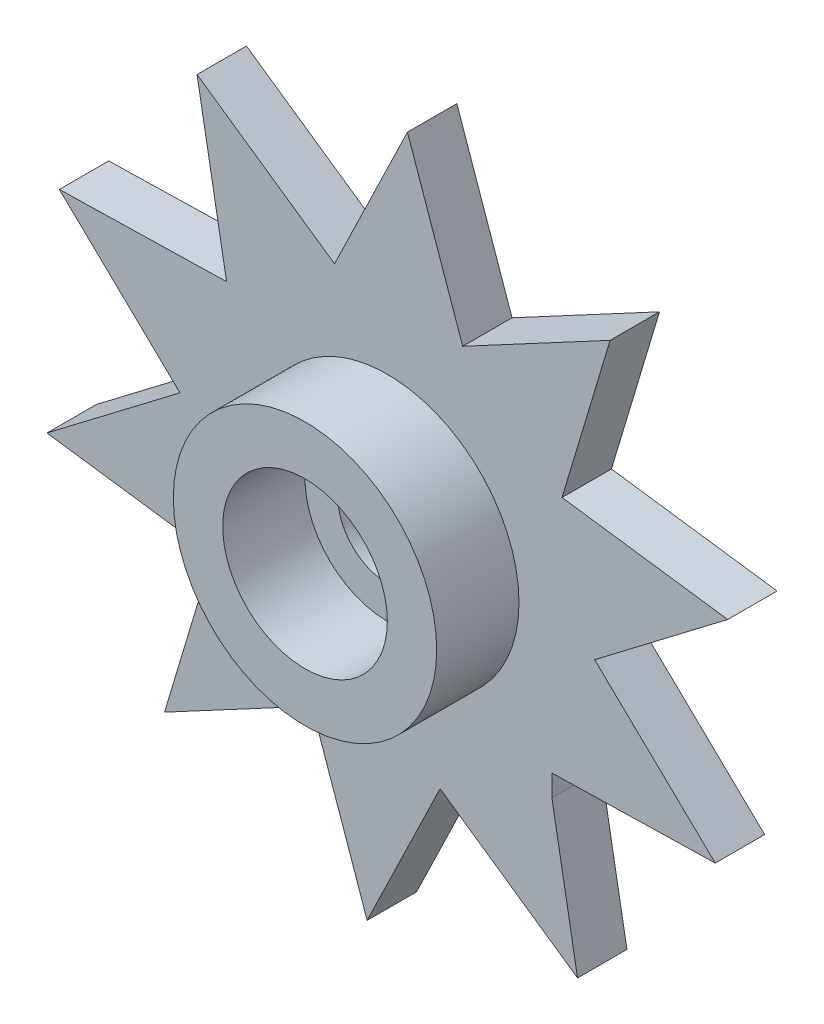
SolidWorks part; units mm, degrees
ref_plane "Plan de face" through (0, 0, 0) normal (0, 0, 1) x (1, 0, 0)
ref_plane "Plan de dessus" through (0, 0, 0) normal (0, 1, 0) x (1, 0, 0)
ref_plane "Plan de droite" through (0, 0, 0) normal (1, 0, 0) x (0, 0, -1)
sketch "Esquisse1" plane through (0, 0, 0) normal (0, 0, 1) x (1, 0, 0)
  line L0 (-27.0978, 20.4024) -> (-22.9222, 17.51)
  line L1 (-22.9222, 17.51) -> (-23.8175, 22.51)
  line L2 (-23.8175, 22.51) -> (-18.7392, 22.6243)
  line L3 (-18.7392, 22.6243) -> (-22.4024, 26.1432)
  line L4 (-22.4024, 26.1432) -> (-18.3613, 29.2206)
  line L5 (-18.3613, 29.2206) -> (-23.3932, 29.9142)
  line L6 (-23.3932, 29.9142) -> (-21.9327, 34.7792)
  line L7 (-21.9327, 34.7792) -> (-26.4113, 32.3827)
  line L8 (-26.4113, 32.3827) -> (-28.0893, 37.1771)
  line L9 (-28.0893, 37.1771) -> (-30.304, 32.6058)
  line L10 (-30.304, 32.6058) -> (-34.4795, 35.4982)
  line L11 (-34.4795, 35.4982) -> (-33.5843, 30.4982)
  line L12 (-33.5843, 30.4982) -> (-38.6625, 30.3839)
  line L13 (-38.6625, 30.3839) -> (-34.9993, 26.865)
  line L14 (-34.9993, 26.865) -> (-39.0405, 23.7876)
  line L15 (-39.0405, 23.7876) -> (-34.0086, 23.0939)
  line L16 (-34.0086, 23.0939) -> (-35.4691, 18.2289)
  line L17 (-35.4691, 18.2289) -> (-30.9904, 20.6254)
  line L18 (-30.9904, 20.6254) -> (-29.3124, 15.8311)
  line L19 (-29.3124, 15.8311) -> (-27.0978, 20.4024)
extrude "Boss.-Extru.1" add sketch "Esquisse1" against normal blind 1.5
ref_plane "Plan1" through (0, 26.5041, 0) normal (0, -1, 0) x (1, 0, 0)
sketch "Esquisse2" plane through (0, 26.5041, 0) normal (0, -1, 0) x (1, 0, 0)
  line L0 (-24.7009, 2.5) -> (-28.7009, 2.5)
  line L1 (-28.7009, 2.5) -> (-28.7009, 0)
  line L2 (-28.7009, 0) -> (-24.7009, 0)
  line L3 (-24.7009, 0) -> (-24.7009, 2.5)
  line L4 (-28.7009, 2.5) -> (-28.7009, 0) construction
revolve "Révolution1" add sketch "Esquisse2" angle 360 about L4
hole_wizard "Chambrage pour vis à tête hexagonale M2.51" positions "Esquisse4" profile "Esquisse3" counterbore size "M2.5" standard "Ansi Métrique"
sketch "Esquisse4" plane through (0, 0, 2.5) normal (0, 0, 1) x (1, 0, 0)
  point P0 (-28.7009, 26.5041)
sketch "Esquisse3" plane through (-28.7009, 26.5041, 2.5) normal (1, 0, 0) x (0, -1, 0)
  line L0 (0, 0) -> (0, 4)
  line L1 (0, 4) -> (1.5, 4)
  line L3 (1.5, 4) -> (1.5, 2.5)
  line L4 (1.5, 2.5) -> (2.5, 2.5)
  line L5 (2.5, 2.5) -> (2.5, 0)
  line L7 (2.5, 0) -> (0, 0)
  line L11 (0, -6.35) -> (0, 107.95) construction
  dimension "Diamètre du perçage jusqu'au prochain" = 3
  dimension "Profondeur du perçage jusqu'au prochain" = 4
  dimension "Diamètre du chambrage" = 5
  dimension "Profondeur du chambrage" = 2.5
chamfer "Chanfrein1" distance 0.6615 angle 10.151 1 edges at (-23.8175, 22.51, -0.75)
